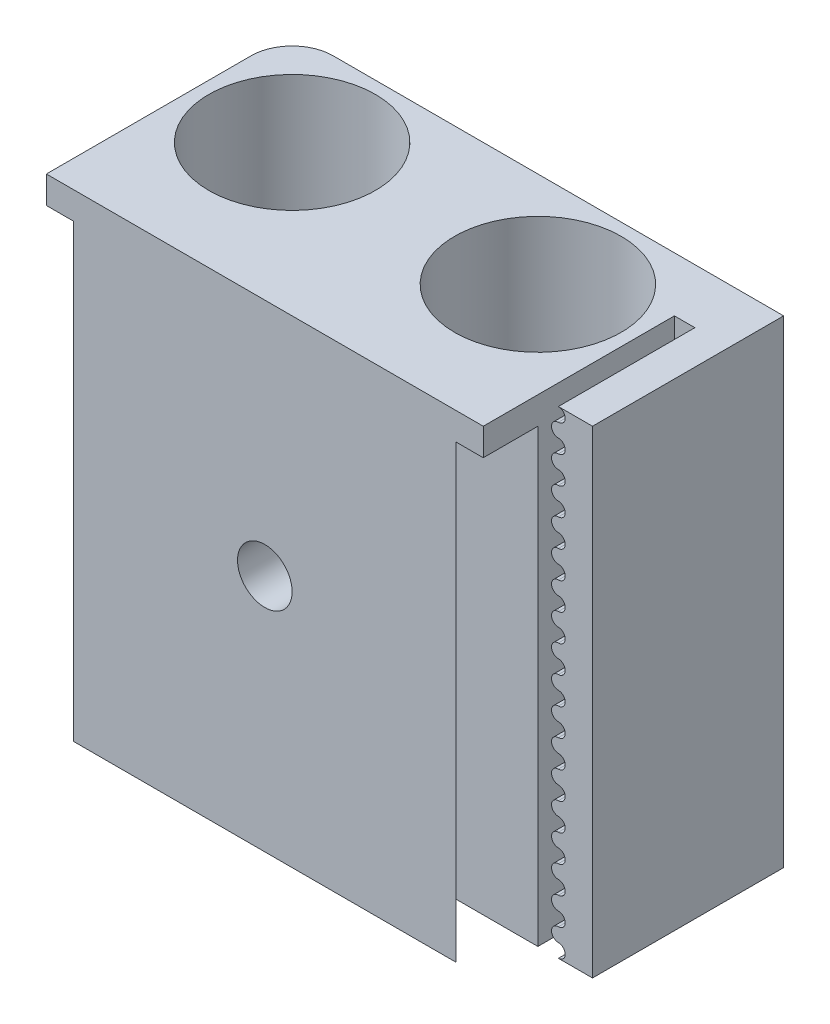
SolidWorks part; units mm, degrees
ref_plane "Спереди" through (0, 0, 0) normal (0, 0, 1) x (1, 0, 0)
ref_plane "Сверху" through (0, 0, 0) normal (0, 1, 0) x (1, 0, 0)
ref_plane "Справа" through (0, 0, 0) normal (1, 0, 0) x (0, 0, -1)
sketch "Эскиз1" plane through (0, 0, 0) normal (0, 0, 1) x (1, 0, 0)
  line L1 (-16, 17.5) -> (16, 17.5)
  line L2 (-16, 17.5) -> (-16, -17.5)
  line L3 (-16, -17.5) -> (16, -17.5)
  line L4 (16, 17.5) -> (16, -17.5)
  line L5 (-16, 17.5) -> (16, -17.5) construction
  line L6 (-16, -17.5) -> (16, 17.5) construction
  point P0 (0, 0)
  dimension "D1" = 32
  dimension "D2" = 35
extrude "Бобышка-Вытянуть1" add sketch "Эскиз1" along normal blind 14
sketch "Эскиз2" plane through (0, 17.5, 0) normal (0, 1, 0) x (1, 0, 0)
  line L0 (0, 0) -> (0, -14) construction
  line L1 (16, 0) -> (-16, 0) construction
  line L2 (16, -14) -> (-16, -14) construction
  circle A0 centre (-9, -7) radius 6.1
  circle A1 centre (9, -7) radius 6.1
  dimension "D1" = 9
extrude "Вырез-Вытянуть1" cut sketch "Эскиз2" against normal up to next
sketch "Эскиз3" plane through (0, -17.5, 0) normal (0, 1, 0) x (1, 0, 0)
  line L0 (-14, -18) -> (-10, -14)
  line L1 (-10, -14) -> (10, -14)
  line L3 (-14, -18) -> (14, -18)
  line L5 (14, -18) -> (10, -14)
  line L6 (0, 0) -> (0, -18) construction
  dimension "D1" = 4
  dimension "D2" = 45
  dimension "D3" = 45
  dimension "D4" = 28
extrude "Бобышка-Вытянуть2" add sketch "Эскиз3" along normal blind 33
sketch "Эскиз5" plane through (0, 15.5, 0) normal (0, 1, 0) x (-1, 0, 0)
  line L1 (16, 14) -> (-16, 14)
  line L2 (16, 14) -> (16, 18)
  line L3 (16, 18) -> (-16, 18)
  line L4 (-16, 14) -> (-16, 18)
fillet "Скругление1" radius 3 1 edges at (-16, 0, 0)
sketch "Эскиз6" plane through (16, 0, 0) normal (1, 0, 0) x (0, 0, -1)
  line L0 (-14, -17.5) -> (0, -17.5) construction
  line L1 (0, 17.5) -> (-14, 17.5)
  line L2 (0, 17.5) -> (0, -17.5)
  line L3 (0, -17.5) -> (-14, -17.5)
  line L4 (-14, 17.5) -> (-14, -17.5)
extrude "Бобышка-Вытянуть4" add sketch "Эскиз6" along normal blind 4
sketch "Эскиз7" plane through (0, 0, 14) normal (0, 0, 1) x (1, 0, 0)
  line L0 (16, -17.5) -> (17.5, -17.5)
  line L2 (16, -17.5) -> (16, 17.5)
  line L3 (16, 17.5) -> (17.5, 17.5)
  line L5 (17.5, 17.5) -> (17.5, -17.5) construction
  arc A0 (17.5, 16.5) -> (17.5, 17.5) centre (17.5, 17) ccw
  arc A1 (17.5, 16.5) -> (17.5, 15.5) centre (17.5, 16) ccw
  arc A2 (17.5, 14.5) -> (17.5, 15.5) centre (17.5, 15) ccw
  arc A3 (17.5, 14.5) -> (17.5, 13.5) centre (17.5, 14) ccw
  arc A4 (17.5, 12.5) -> (17.5, 13.5) centre (17.5, 13) ccw
  arc A5 (17.5, 12.5) -> (17.5, 11.5) centre (17.5, 12) ccw
  arc A6 (17.5, 10.5) -> (17.5, 11.5) centre (17.5, 11) ccw
  arc A7 (17.5, 10.5) -> (17.5, 9.5) centre (17.5, 10) ccw
  arc A8 (17.5, 8.5) -> (17.5, 9.5) centre (17.5, 9) ccw
  arc A9 (17.5, 8.5) -> (17.5, 7.5) centre (17.5, 8) ccw
  arc A10 (17.5, 6.5) -> (17.5, 7.5) centre (17.5, 7) ccw
  arc A11 (17.5, 6.5) -> (17.5, 5.5) centre (17.5, 6) ccw
  arc A12 (17.5, 4.5) -> (17.5, 5.5) centre (17.5, 5) ccw
  arc A13 (17.5, 4.5) -> (17.5, 3.5) centre (17.5, 4) ccw
  arc A14 (17.5, 2.5) -> (17.5, 3.5) centre (17.5, 3) ccw
  arc A15 (17.5, 2.5) -> (17.5, 1.5) centre (17.5, 2) ccw
  arc A16 (17.5, 0.5) -> (17.5, 1.5) centre (17.5, 1) ccw
  arc A17 (17.5, 0.5) -> (17.5, -0.5) centre (17.5, 0) ccw
  arc A18 (17.5, -1.5) -> (17.5, -0.5) centre (17.5, -1) ccw
  arc A19 (17.5, -1.5) -> (17.5, -2.5) centre (17.5, -2) ccw
  arc A20 (17.5, -3.5) -> (17.5, -2.5) centre (17.5, -3) ccw
  arc A21 (17.5, -3.5) -> (17.5, -4.5) centre (17.5, -4) ccw
  arc A22 (17.5, -5.5) -> (17.5, -4.5) centre (17.5, -5) ccw
  arc A23 (17.5, -5.5) -> (17.5, -6.5) centre (17.5, -6) ccw
  arc A24 (17.5, -7.5) -> (17.5, -6.5) centre (17.5, -7) ccw
  arc A25 (17.5, -7.5) -> (17.5, -8.5) centre (17.5, -8) ccw
  arc A26 (17.5, -9.5) -> (17.5, -8.5) centre (17.5, -9) ccw
  arc A27 (17.5, -9.5) -> (17.5, -10.5) centre (17.5, -10) ccw
  arc A28 (17.5, -11.5) -> (17.5, -10.5) centre (17.5, -11) ccw
  arc A29 (17.5, -11.5) -> (17.5, -12.5) centre (17.5, -12) ccw
  arc A30 (17.5, -13.5) -> (17.5, -12.5) centre (17.5, -13) ccw
  arc A31 (17.5, -13.5) -> (17.5, -14.5) centre (17.5, -14) ccw
  arc A32 (17.5, -15.5) -> (17.5, -14.5) centre (17.5, -15) ccw
  arc A33 (17.5, -15.5) -> (17.5, -16.5) centre (17.5, -16) ccw
  arc A34 (17.5, -17.5) -> (17.5, -16.5) centre (17.5, -17) ccw
  arc A36 (17.5, -17.5) -> (17.5, -18.5) centre (17.5, -18) ccw [skipped]
  dimension "D2" = 0.5
  dimension "D1" = 1.5
  dimension "D3" = 18
extrude "Вырез-Вытянуть2" cut sketch "Эскиз7" against normal blind 10
extrude "Бобышка-Вытянуть5" add sketch "Эскиз5" along normal blind 2
sketch "Эскиз8" plane through (0, 0, 18) normal (0, 0, 1) x (1, 0, 0)
  circle A0 centre (0, 0) radius 2
extrude "Вырез-Вытянуть3" cut sketch "Эскиз8" against normal up to next
sketch "Эскиз9" plane through (0, 0, 0) normal (0, 0, -1) x (-1, 0, 0)
  line L1 (0, -4.0415) -> (3.5, -2.0207)
  line L2 (3.5, -2.0207) -> (3.5, 2.0207)
  line L3 (3.5, 2.0207) -> (0, 4.0415)
  line L4 (0, 4.0415) -> (-3.5, 2.0207)
  line L5 (-3.5, 2.0207) -> (-3.5, -2.0207)
  line L6 (-3.5, -2.0207) -> (0, -4.0415)
  circle A0 centre (0, 0) radius 3.5 construction
extrude "Вырез-Вытянуть4" cut sketch "Эскиз9" against normal blind 3.5
